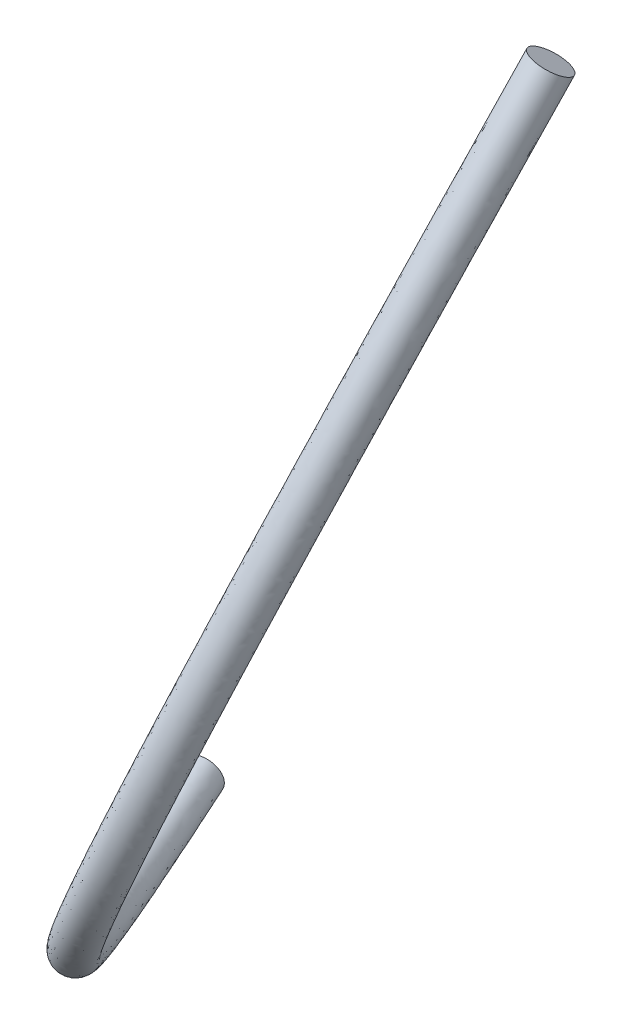
SolidWorks part; units mm, degrees
ref_plane "前视基准面" through (0, 0, 0) normal (0, 0, 1) x (1, 0, 0)
ref_plane "上视基准面" through (0, 0, 0) normal (0, 1, 0) x (1, 0, 0)
ref_plane "右视基准面" through (0, 0, 0) normal (1, 0, 0) x (0, 0, -1)
sketch3d "3D草图1"
  line L0 (64, 132.5025, 9.5626) -> (64, 148.9031, 9.5626) construction
  spline S0 degree 2 poles (0, 0, 0) (31.6183, -16.4904, 88.9147) (64, 132.5025, 9.5626) knots 0 0 0 1 1 1
sweep "扫描1" add path "3D草图1" circular profile diameter 6 parameters "D3"=6
